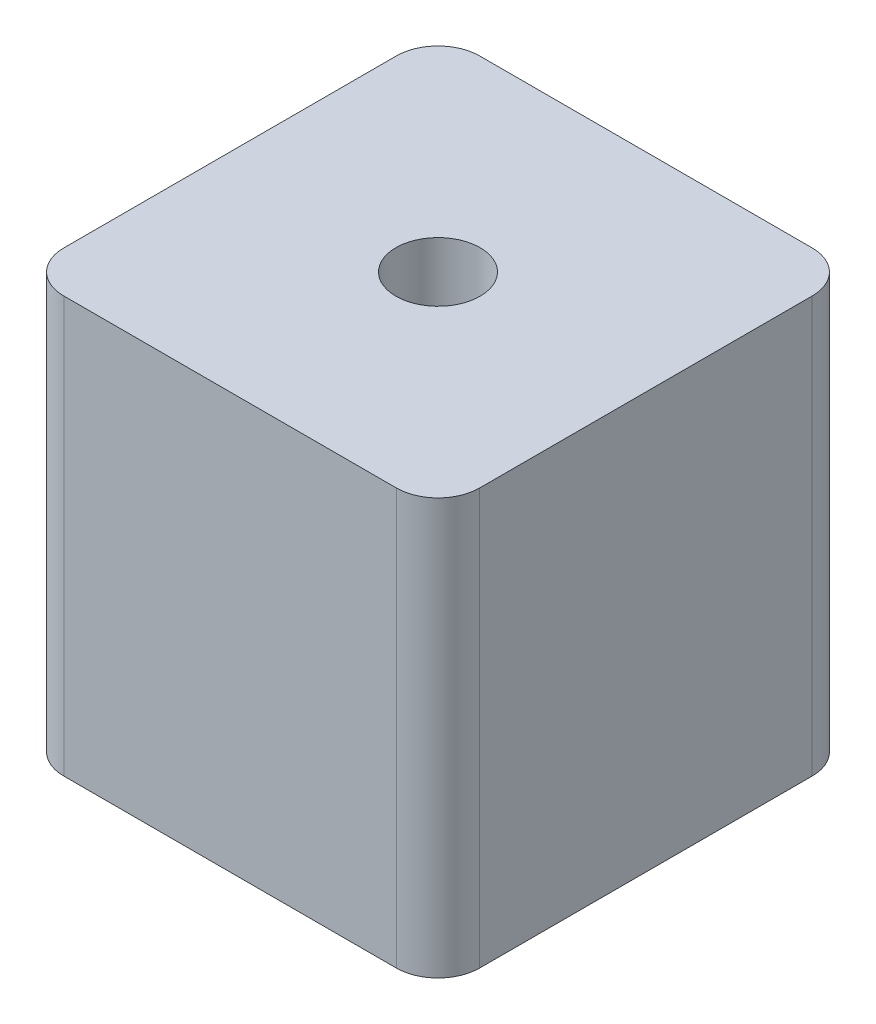
SolidWorks part; units mm, degrees
ref_plane "前视基准面" through (0, 0, 0) normal (0, 0, 1) x (1, 0, 0)
ref_plane "上视基准面" through (0, 0, 0) normal (0, 1, 0) x (1, 0, 0)
ref_plane "右视基准面" through (0, 0, 0) normal (1, 0, 0) x (0, 0, -1)
other "Configuration Table"
sketch "草图1" plane through (0, 0, 0) normal (0, 1, 0) x (1, 0, 0)
  line L1 (-10, -10) -> (10, -10)
  line L2 (-10, -10) -> (-10, 10)
  line L3 (-10, 10) -> (10, 10)
  line L4 (10, -10) -> (10, 10)
  line L5 (-10, -10) -> (10, 10) construction
  line L6 (-10, 10) -> (10, -10) construction
  point P0 (0, 0)
  dimension "D1" = 20
  dimension "D2" = 20
extrude "凸台-拉伸1" add sketch "草图1" along normal blind 20
sketch "草图2" plane through (0, 20, 0) normal (0, 1, 0) x (1, 0, 0)
  circle A0 centre (0, 0) radius 2.025
  dimension "D1" = 4.05
extrude "切除-拉伸1" cut sketch "草图2" against normal blind 20
fillet "圆角1" radius 2 4 edges at (-10, 10, 10) (-10, 10, -10) (10, 10, -10) (10, 10, 10)
